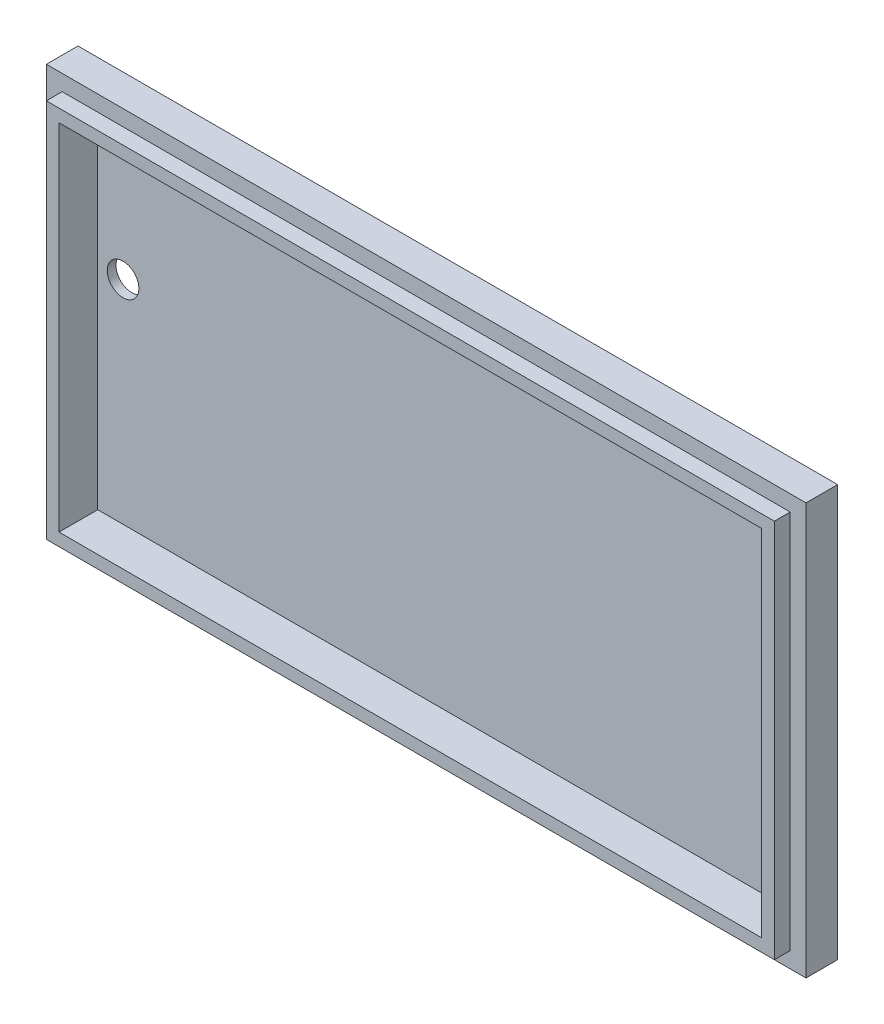
SolidWorks part; units mm, degrees
ref_plane "Front Plane" through (0, 0, 0) normal (0, 0, 1) x (1, 0, 0)
ref_plane "Top Plane" through (0, 0, 0) normal (0, 1, 0) x (1, 0, 0)
ref_plane "Right Plane" through (0, 0, 0) normal (1, 0, 0) x (0, 0, -1)
ref_plane "Plane1" through (0, 0, 2.5) normal (0, 0, 1) x (1, 0, 0)
sketch "Sketch1" plane through (0, 0, 2.5) normal (0, 0, 1) x (1, 0, 0)
  line L0 (0, 0) -> (120, 0)
  line L1 (120, 0) -> (120, 65)
  line L2 (120, 65) -> (0, 65)
  line L3 (0, 65) -> (0, 0)
extrude "Boss-Extrude1" add sketch "Sketch1" against normal blind 5
sketch "Sketch2" plane through (0, 0, 2.5) normal (0, 0, 1) x (1, 0, 0)
  line L0 (117.5, 2.5) -> (2.5, 2.5)
  line L1 (2.5, 2.5) -> (2.5, 62.5)
  line L2 (2.5, 62.5) -> (117.5, 62.5)
  line L3 (117.5, 62.5) -> (117.5, 2.5)
extrude "Boss-Extrude2" add sketch "Sketch2" along normal blind 2.5
hole_wizard "Ø5.0 (5) Diameter Hole1" positions "Sketch4" profile "Sketch3" hole size "Ø5.0" standard "ANSI Metric"
sketch "Sketch4" plane through (0, 0, -2.5) normal (0, 0, -1) x (-1, 0, 0)
  line L0 (0, 65) -> (0, 0) construction
  line L1 (-120, 65) -> (0, 65) construction
  point P0 (-8.5, 38)
  dimension "D1" = 8.5
  dimension "D2" = 27
sketch "Sketch3" plane through (8.5, 38, -2.5) normal (1, 0, 0) x (0, 1, 0)
  line L0 (0, 0) -> (0, 7.5)
  line L1 (0, 7.5) -> (2.5, 7.5)
  line L2 (2.5, 7.5) -> (2.5, 0)
  line L5 (2.5, 0) -> (0, 0)
  line L11 (0, -6.35) -> (0, 107.95) construction
  dimension "Thru Hole Dia." = 5
  dimension "Thru Hole Depth" = 7.5
sketch "Sketch5" plane through (0, 0, 5) normal (0, 0, 1) x (1, 0, 0)
  line L1 (4.5, 60.5) -> (115.5, 60.5)
  line L2 (4.5, 60.5) -> (4.5, 4.5)
  line L3 (4.5, 4.5) -> (115.5, 4.5)
  line L4 (115.5, 60.5) -> (115.5, 4.5)
  point P4 (2.5, 62.5)
  point P5 (2.5, 2.5)
  point P7 (117.5, 2.5)
  point P9 (117.5, 62.5)
  dimension "D1" = 2
  dimension "D2" = 2
  dimension "D3" = 2
  dimension "D4" = 2
extrude "Cut-Extrude3" cut sketch "Sketch5" against normal blind 6.12 contours L2 L1 L4 L3
